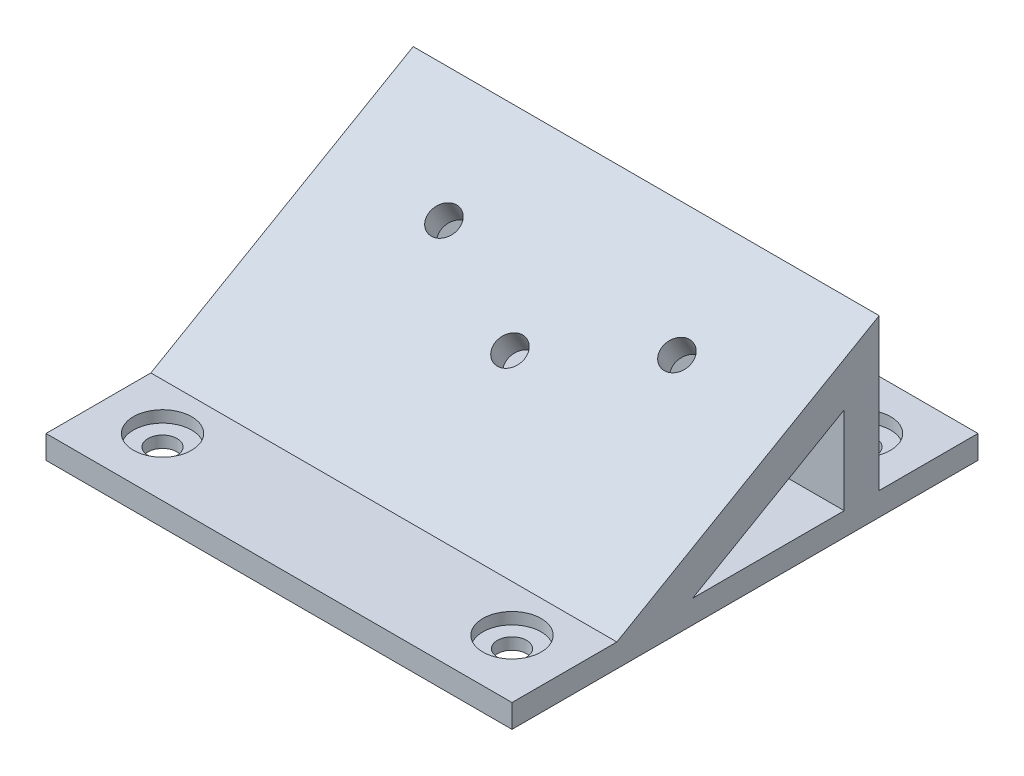
SolidWorks part; units mm, degrees
ref_plane "Front Plane" through (0, 0, 0) normal (0, 0, 1) x (1, 0, 0)
ref_plane "Top Plane" through (0, 0, 0) normal (0, 1, 0) x (1, 0, 0)
ref_plane "Right Plane" through (0, 0, 0) normal (1, 0, 0) x (0, 0, -1)
sketch "Sketch1" plane through (0, 0, 0) normal (0, 1, 0) x (1, 0, 0)
  line L1 (-32.0692, 12.3621) -> (7.9308, 12.3621)
  line L2 (-32.0692, 12.3621) -> (-32.0692, -27.6379)
  line L3 (-32.0692, -27.6379) -> (7.9308, -27.6379)
  line L4 (7.9308, 12.3621) -> (7.9308, -27.6379)
  dimension "D1" = 40
  dimension "D2" = 40
extrude "Boss-Extrude1" add sketch "Sketch1" along normal blind 2
sketch "Sketch2" plane through (0, 2, 0) normal (0, 1, 0) x (1, 0, 0)
  line L0 (7.9308, 12.3621) -> (-32.0692, 12.3621) construction
  line L1 (-32.0692, 12.3621) -> (-32.0692, -27.6379) construction
  line L2 (7.9308, -27.6379) -> (7.9308, 12.3621) construction
  line L3 (-32.0692, -27.6379) -> (7.9308, -27.6379) construction
  circle A0 centre (-27.0692, -22.6379) radius 1.25
  circle A1 centre (-27.0692, 7.3621) radius 1.25
  circle A2 centre (2.9308, 7.3621) radius 1.25
  circle A3 centre (2.9308, -22.6379) radius 1.25
  dimension "D1" = 2.5
  dimension "D2" = 2.5
  dimension "D3" = 2.5
  dimension "D4" = 2.5
  dimension "D5" = 30
  dimension "D7" = 30
  dimension "D8" = 30
  dimension "D9" = 5
  dimension "D10" = 5
  dimension "D11" = 5
  dimension "D12" = 5
  dimension "D6" = 30
extrude "Cut-Extrude1" cut sketch "Sketch2" against normal through all
sketch "Sketch4" plane through (7.9308, 0, 0) normal (1, 0, 0) x (0, 0, -1)
  line L0 (-18.6379, 2) -> (3.8787, 2)
  line L1 (-27.6379, 2) -> (12.3621, 2) construction
  line L2 (3.8787, 15) -> (-18.6379, 2)
  line L3 (3.8787, 15) -> (3.8787, 2)
  point P4 (0, 0)
  point P6 (0, 0)
  point P8 (0, 0)
  point P9 (-14.0887, 8.1705)
  point P10 (0, 0)
  point P11 (0, 0)
  point P12 (3.866, 2)
  point P13 (0, 0)
  point P14 (0, 0)
  point P15 (0, 0)
  dimension "D1" = 30
  dimension "D2" = 26
  dimension "D3" = 60
  dimension "D4" = 9
extrude "Boss-Extrude2" add sketch "Sketch4" against normal blind 40 contours L0 L3 L2
sketch "Sketch5" plane through (0, 2, 0) normal (0, 1, 0) x (1, 0, 0)
  circle A0 centre (2.9308, 7.3621) radius 2.5
  circle A1 centre (2.9308, 7.3621) radius 1.25 construction
  circle A2 centre (2.9308, -22.6379) radius 2.5
  circle A3 centre (2.9308, -22.6379) radius 1.25 construction
  circle A4 centre (37.902, 5.85) radius 2.5
  circle A5 centre (-27.0692, 7.3621) radius 2.5
  circle A6 centre (-27.0692, 7.3621) radius 1.25 construction
  circle A7 centre (-27.0692, -22.6379) radius 2.5
  circle A8 centre (-27.0692, -22.6379) radius 1.25 construction
  dimension "D1" = 5
sketch "Sketch6" plane through (0, 9.5705, 5.5255) normal (0, 0.866, 0.5) x (1, 0, 0)
  line L0 (7.9308, 10.8591) -> (7.9308, -15.1409) construction
  line L1 (-32.0692, 10.8591) -> (7.9308, 10.8591) construction
  circle A0 centre (-22.0692, 2.3591) radius 1.25
  circle A1 centre (-12.0692, -2.6409) radius 1.25
  circle A2 centre (-2.0692, 2.3591) radius 1.25
  dimension "D1" = 2.5
  dimension "D2" = 2.5
  dimension "D3" = 2.5
  dimension "D4" = 20
  dimension "D5" = 10
  dimension "D6" = 5
  dimension "D7" = 5
  dimension "D8" = 10
  dimension "D9" = 8.5
extrude "Cut-Extrude3" cut sketch "Sketch5" against normal blind 1
sketch "Sketch9" plane through (7.9308, 0, 0) normal (1, 0, 0) x (0, 0, -1)
  line L0 (-12.1213, 2) -> (0.8787, 2)
  line L1 (3.8787, 2) -> (12.3621, 2) construction
  line L2 (-12.1213, 2) -> (0.8787, 9.5056)
  line L3 (0.8787, 9.5056) -> (0.8787, 2)
  line L5 (3.8787, 15) -> (3.8787, 2) construction
  point P4 (0, 0)
  point P7 (0, 0)
  dimension "D1" = 30
  dimension "D2" = 60
  dimension "D3" = 13
  dimension "D4" = 3
extrude "Cut-Extrude4" cut sketch "Sketch9" against normal through all contours L0 L3 L2
extrude "Cut-Extrude5" cut sketch "Sketch6" against normal up to body separate body
sketch "Sketch11" plane through (0, 6.7487, 3.8963) normal (0, -0.866, -0.5) x (-1, 0, 0)
  circle A0 centre (2.0692, 2.3591) radius 2.6
  circle A1 centre (2.0692, 2.3591) radius 1.25 construction
  circle A2 centre (22.0692, 2.3591) radius 2.6
  circle A3 centre (12.0692, -2.6409) radius 2.6
  circle A4 centre (12.0692, -2.6409) radius 1.25 construction
  circle A5 centre (22.0692, 2.3591) radius 1.25 construction
  dimension "D1" = 5.2
  dimension "D2" = 5.2
  dimension "D3" = 5.2
extrude "Cut-Extrude6" cut sketch "Sketch11" against normal blind 1.2 contours A2 | A0 | A3
